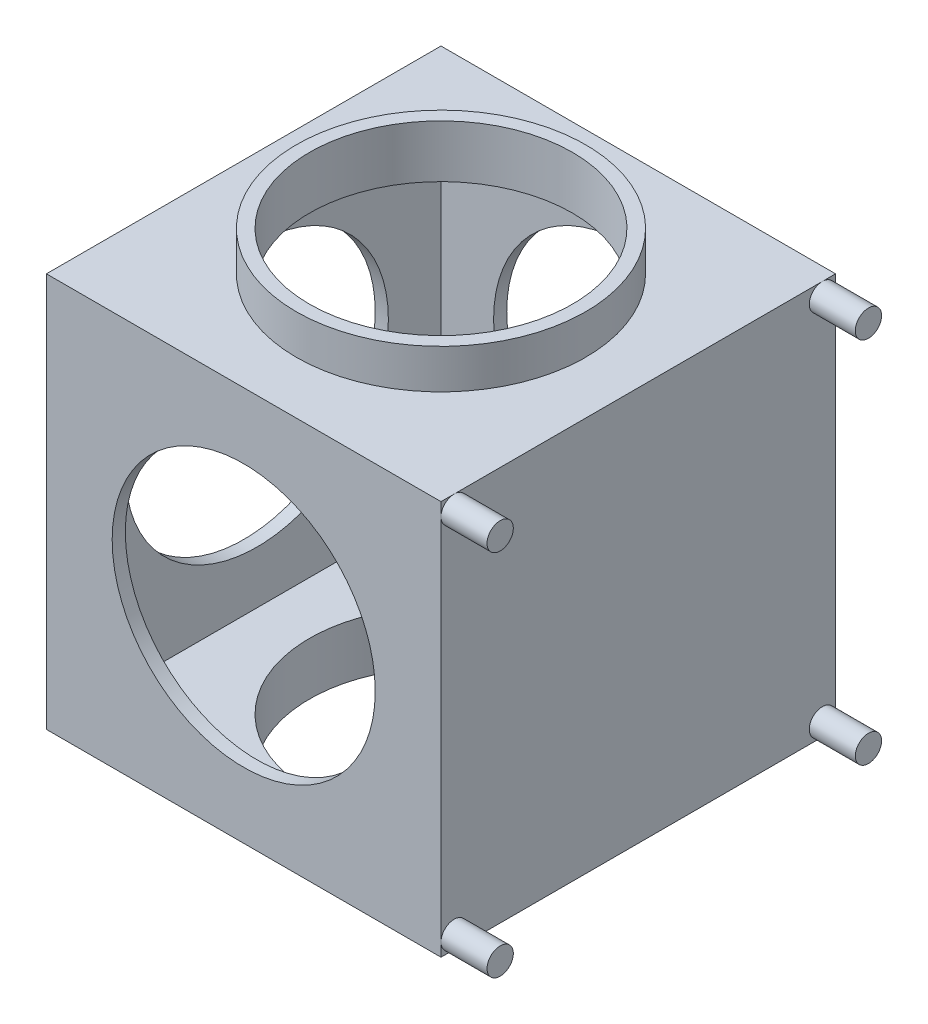
SolidWorks part; units mm, degrees
material "Commercial Bronze, UNS C22000 (90-10 Bronze)"
ref_plane "Front Plane" through (0, 0, 0) normal (0, 0, 1) x (1, 0, 0)
ref_plane "Top Plane" through (0, 0, 0) normal (0, 1, 0) x (1, 0, 0)
ref_plane "Right Plane" through (0, 0, 0) normal (1, 0, 0) x (0, 0, -1)
sketch "Sketch1" plane through (0, 0, 0) normal (0, 1, 0) x (1, 0, 0)
  line L1 (-150, 150) -> (150, 150)
  line L2 (-150, 150) -> (-150, -150)
  line L3 (-150, -150) -> (150, -150)
  line L4 (150, 150) -> (150, -150)
  line L5 (-150, 150) -> (150, -150) construction
  line L6 (-150, -150) -> (150, 150) construction
  point P0 (0, 0)
extrude "Boss-Extrude1" add sketch "Sketch1" along normal blind 300
sketch "Sketch2" plane through (0, 300, 0) normal (0, 1, 0) x (1, 0, 0)
  line L1 (-140, 140) -> (140, 140)
  line L2 (-140, 140) -> (-140, -140)
  line L3 (-140, -140) -> (140, -140)
  line L4 (140, 140) -> (140, -140)
  line L5 (-140, 140) -> (140, -140) construction
  line L6 (-140, -140) -> (140, 140) construction
  point P0 (0, 0)
extrude "Cut-Extrude1" cut sketch "Sketch2" against normal blind 290
sketch "Sketch5" plane through (0, 300, 0) normal (0, 1, 0) x (1, 0, 0)
  line L1 (-150, -150) -> (150, -150)
  line L2 (-150, -150) -> (-150, 150)
  line L3 (-150, 150) -> (150, 150)
  line L4 (150, -150) -> (150, 150)
  line L5 (-150, -150) -> (150, 150) construction
  line L6 (-150, 150) -> (150, -150) construction
  point P0 (0, 0)
extrude "Boss-Extrude3" add sketch "Sketch5" against normal blind 10
sketch "Sketch6" plane through (0, 300, 0) normal (0, 1, 0) x (1, 0, 0)
  circle A0 centre (0, 0) radius 100
extrude "Cut-Extrude3" cut sketch "Sketch6" against normal through all
sketch "Sketch7" plane through (0, 0, -150) normal (0, 0, -1) x (-1, 0, 0)
  line L0 (0, 300) -> (0, 0)
  line L1 (-150, 300) -> (150, 300) construction
  line L2 (-150, 0) -> (150, 0) construction
  circle A0 centre (0, 150) radius 100
extrude "Cut-Extrude4" cut sketch "Sketch7" against normal through all contours L0 A0 | L0 A0
sketch "Sketch8" plane through (-150, 0, 0) normal (-1, 0, 0) x (0, 0, 1)
  line L0 (0, 0) -> (0, 300)
  line L1 (-150, 0) -> (150, 0) construction
  line L2 (-150, 300) -> (150, 300) construction
  circle A0 centre (0, 150) radius 100
extrude "Cut-Extrude5" cut sketch "Sketch8" against normal blind 10 contours L0 A0 | L0 A0
sketch "Sketch9" plane through (150, 0, 0) normal (1, 0, 0) x (0, 0, -1)
  line L0 (-140, 20) -> (-140, 0)
  line L1 (-150, 0) -> (-130, 0)
  line L2 (-150, 0) -> (-150, 20)
  line L3 (-150, 20) -> (-130, 20)
  line L4 (-130, 0) -> (-130, 20)
  line L5 (0, 0) -> (0, 300)
  line L6 (-150, 300) -> (150, 300) construction
  circle A0 centre (-140, 10) radius 10
  circle A1 centre (-140, 290) radius 10
  circle A2 centre (140, 290) radius 10
  circle A3 centre (140, 10) radius 10
  point P14 (0, 150)
  point P26 (0, 150)
  dimension "D1" = 4
extrude "Boss-Extrude4" add sketch "Sketch9" along normal blind 35 contours A2 | A3 | A1 | L0 A0 | A0 L0
sketch "Sketch10" plane through (0, 300, 0) normal (0, 1, 0) x (1, 0, 0)
  circle A0 centre (0, 0) radius 100
  circle A1 centre (0, 0) radius 110
extrude "Boss-Extrude5" add sketch "Sketch10" along normal blind 30
sketch "Sketch11" plane through (0, 0, 0) normal (0, -1, 0) x (1, 0, 0)
  circle A0 centre (0, 0) radius 100
  circle A1 centre (0, 0) radius 110
extrude "Boss-Extrude6" add sketch "Sketch11" along normal blind 30
